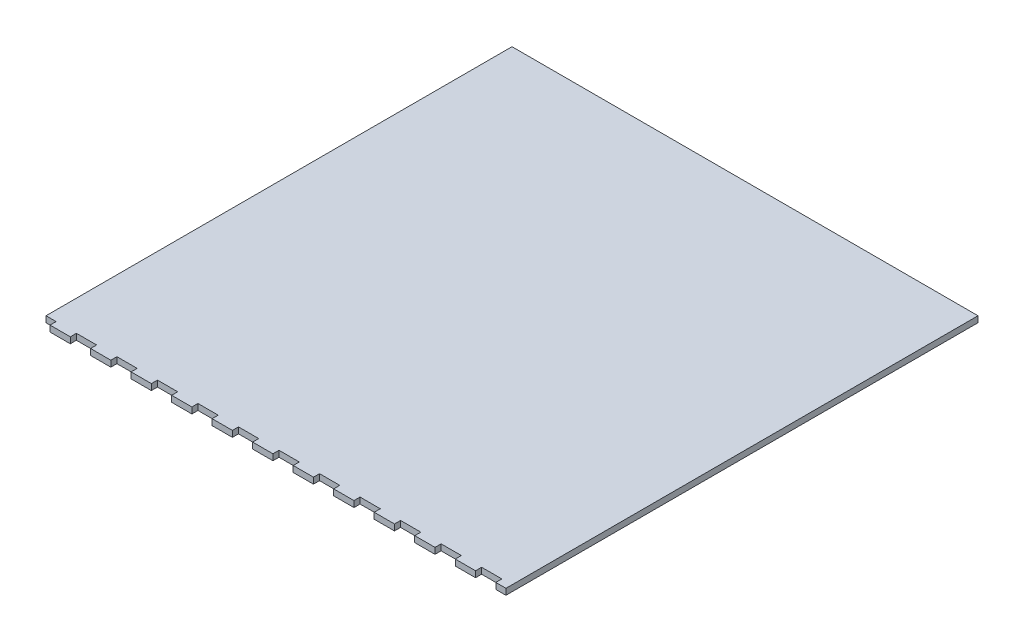
SolidWorks part; units mm, degrees
material "Chêne"
ref_plane "Plan de face" through (0, 0, 0) normal (0, 0, 1) x (1, 0, 0)
ref_plane "Plan de dessus" through (0, 0, 0) normal (0, 1, 0) x (1, 0, 0)
ref_plane "Plan de droite" through (0, 0, 0) normal (1, 0, 0) x (0, 0, -1)
sketch "Esquisse1" plane through (0, 0, 0) normal (0, 1, 0) x (1, 0, 0)
  line L1 (0, 0) -> (230, 0)
  line L2 (0, 0) -> (0, 233)
  line L3 (0, 233) -> (230, 233)
  line L4 (230, 0) -> (230, 233)
  dimension "D1" = 233
  dimension "D2" = 230
extrude "Base" add sketch "Esquisse1" along normal blind 3
sketch "Esquisse2" plane through (0, 3, 0) normal (0, 1, 0) x (1, 0, 0)
  line L0 (0, 0) -> (230, 0) construction
  line L1 (115, 0) -> (125, 0)
  line L2 (115, 0) -> (115, 3)
  line L3 (115, 3) -> (125, 3)
  line L4 (125, 0) -> (125, 3)
  line L5 (135, 3) -> (145, 3)
  line L6 (135, 0) -> (135, 3)
  line L7 (135, 0) -> (145, 0)
  line L8 (145, 0) -> (145, 3)
  line L9 (155, 3) -> (165, 3)
  line L10 (155, 0) -> (155, 3)
  line L11 (155, 0) -> (165, 0)
  line L12 (165, 0) -> (165, 3)
  line L13 (175, 3) -> (185, 3)
  line L14 (175, 0) -> (175, 3)
  line L15 (175, 0) -> (185, 0)
  line L16 (185, 0) -> (185, 3)
  line L17 (195, 3) -> (205, 3)
  line L18 (195, 0) -> (195, 3)
  line L19 (195, 0) -> (205, 0)
  line L20 (205, 0) -> (205, 3)
  line L21 (215, 3) -> (225, 3)
  line L22 (215, 0) -> (215, 3)
  line L23 (215, 0) -> (225, 0)
  line L24 (225, 0) -> (225, 3)
  line L25 (95, 0) -> (95, 3)
  line L26 (95, 0) -> (105, 0)
  line L27 (105, 0) -> (105, 3)
  line L28 (95, 3) -> (105, 3)
  line L29 (75, 0) -> (75, 3)
  line L30 (75, 0) -> (85, 0)
  line L31 (85, 0) -> (85, 3)
  line L32 (75, 3) -> (85, 3)
  line L33 (55, 0) -> (55, 3)
  line L34 (55, 0) -> (65, 0)
  line L35 (65, 0) -> (65, 3)
  line L36 (55, 3) -> (65, 3)
  line L37 (35, 0) -> (35, 3)
  line L38 (35, 0) -> (45, 0)
  line L39 (45, 0) -> (45, 3)
  line L40 (35, 3) -> (45, 3)
  line L41 (15, 0) -> (15, 3)
  line L42 (15, 0) -> (25, 0)
  line L43 (25, 0) -> (25, 3)
  line L44 (15, 3) -> (25, 3)
  line L45 (-5, 0) -> (-5, 3)
  line L46 (-5, 0) -> (5, 0)
  line L47 (5, 0) -> (5, 3)
  line L48 (-5, 3) -> (5, 3)
  dimension "D1" = 10
  dimension "D2" = 3
  dimension "D3" = 6
  dimension "D4" = 7
extrude "Enlèv. mat.-Extru.1" cut sketch "Esquisse2" against normal up to next
